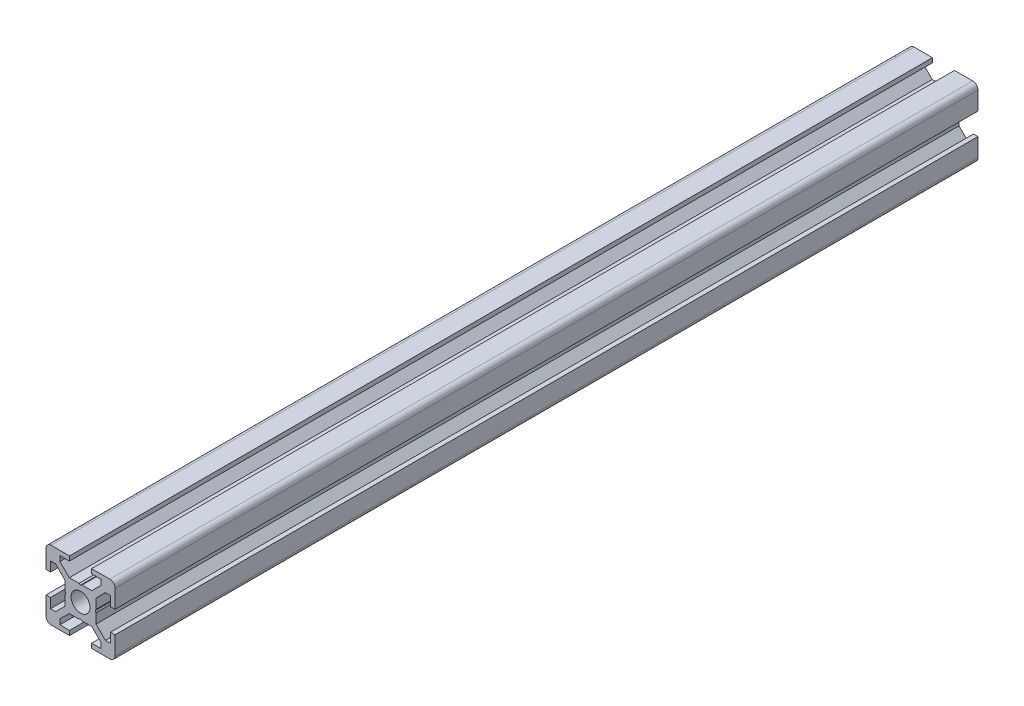
SolidWorks part; units mm, degrees
ref_plane "Front Plane" through (0, 0, 0) normal (0, 0, 1) x (1, 0, 0)
ref_plane "Top Plane" through (0, 0, 0) normal (0, 1, 0) x (1, 0, 0)
ref_plane "Right Plane" through (0, 0, 0) normal (1, 0, 0) x (0, 0, -1)
sketch "Model" plane through (0, 0, 0) normal (0, 0, 1) x (1, 0, 0)
  line L0 (1.5, 20) -> (6.8, 20)
  line L1 (6.8, 20) -> (6.8, 18.7)
  line L2 (6.8, 18.7) -> (4, 18.7)
  line L3 (4, 18.7) -> (4, 17.2)
  line L4 (4, 17.2) -> (6.7458, 14.5)
  line L5 (5.5, 13.2542) -> (5.5, 10.4348)
  line L6 (13.2542, 14.5) -> (16, 17.2)
  line L7 (16, 17.2) -> (16, 18.7)
  line L8 (16, 18.7) -> (13.2, 18.7)
  line L9 (13.2, 18.7) -> (13.2, 20)
  line L10 (13.2, 20) -> (18.5, 20)
  line L11 (20, 18.5) -> (20, 13.2)
  line L12 (20, 13.2) -> (18.7, 13.2)
  line L13 (18.7, 13.2) -> (18.7, 16)
  line L14 (18.7, 16) -> (17.2, 16)
  line L15 (17.2, 16) -> (14.5, 13.2542)
  line L17 (14.5, 6.7458) -> (17.2, 4)
  line L18 (17.2, 4) -> (18.7, 4)
  line L19 (18.7, 4) -> (18.7, 6.8)
  line L20 (18.7, 6.8) -> (20, 6.8)
  line L21 (20, 6.8) -> (20, 1.5)
  line L22 (18.5, 0) -> (13.2, 0)
  line L23 (13.2, 0) -> (13.2, 1.3)
  line L24 (13.2, 1.3) -> (16, 1.3)
  line L25 (16, 1.3) -> (16, 2.7987)
  line L26 (16, 2.7987) -> (13.2541, 5.5)
  line L27 (6.7458, 5.5) -> (9.5652, 5.5)
  line L28 (6.7458, 5.5) -> (4, 2.8)
  line L29 (4, 2.8) -> (4, 1.3)
  line L30 (4, 1.3) -> (6.8, 1.3)
  line L31 (6.8, 1.3) -> (6.8, 0)
  line L32 (6.8, 0) -> (1.5, 0)
  line L33 (0, 1.5) -> (0, 6.8)
  line L34 (0, 6.8) -> (1.3, 6.8)
  line L35 (1.3, 6.8) -> (1.3, 4)
  line L36 (1.3, 4) -> (2.8, 4)
  line L37 (2.8, 4) -> (5.5, 6.7458)
  line L39 (5.5, 13.2542) -> (2.8, 16)
  line L40 (2.8, 16) -> (1.3, 16)
  line L41 (1.3, 16) -> (1.3, 13.2)
  line L42 (1.3, 13.2) -> (0, 13.2)
  line L43 (0, 13.2) -> (0, 18.5)
  line L44 (14.5, 9.5652) -> (14.5, 6.7458)
  line L45 (10.4348, 14.5) -> (13.2542, 14.5)
  line L46 (10, 5.75) -> (9.5652, 5.5)
  line L47 (10, 5.75) -> (10.4348, 5.5)
  line L48 (10.4348, 5.5) -> (13.2541, 5.5)
  line L49 (10, 14.25) -> (10.4348, 14.5)
  line L50 (10, 14.25) -> (9.5652, 14.5)
  line L51 (6.7458, 14.5) -> (9.5652, 14.5)
  line L52 (5.5, 10.4348) -> (5.75, 10)
  line L53 (5.5, 9.5652) -> (5.75, 10)
  line L54 (5.5, 9.5652) -> (5.5, 6.7458)
  line L55 (14.5, 9.5652) -> (14.25, 10)
  line L56 (14.5, 10.4348) -> (14.25, 10)
  line L57 (14.5, 13.2542) -> (14.5, 10.4348)
  circle A0 centre (10, 10) radius 2.75
  arc A1 (18.5, 20) -> (20, 18.5) centre (18.5, 18.5) cw
  arc A2 (20, 1.5) -> (18.5, 0) centre (18.5, 1.5) cw
  arc A3 (1.5, 0) -> (0, 1.5) centre (1.5, 1.5) cw
  arc A4 (0, 18.5) -> (1.5, 20) centre (1.5, 18.5) cw
  dimension "D1" = 1.5
  dimension "D2" = 5.5
  dimension "D4" = 6.4
  dimension "D5" = 12
other "AlignGroup1"
extrude "Boss-Extrude1" add sketch "Model" along normal blind 250
